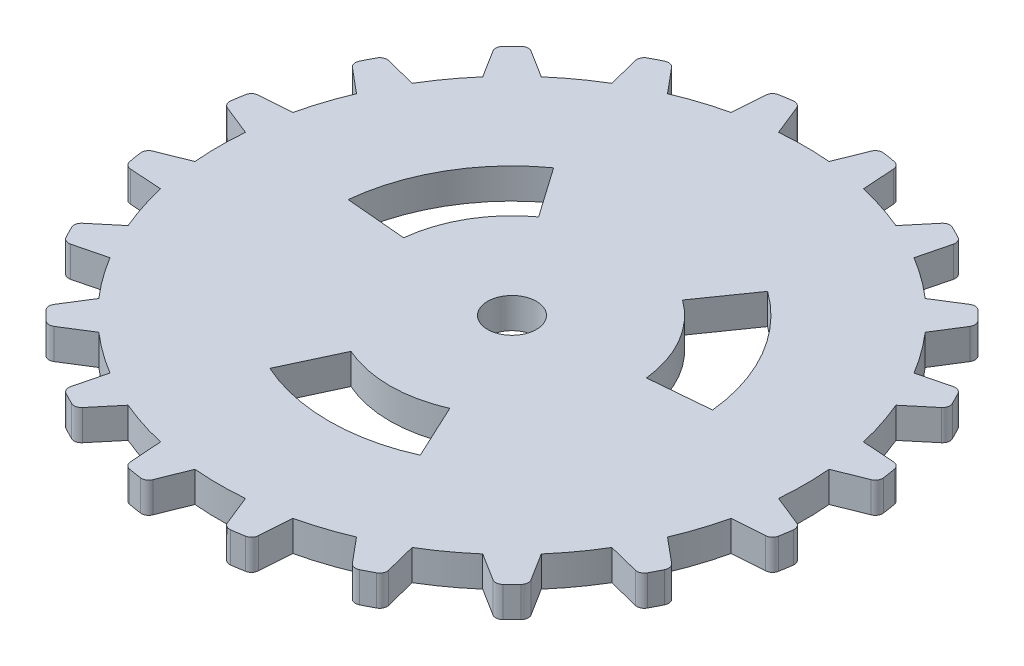
SolidWorks part; units mm, degrees
ref_plane "Front Plane" through (0, 0, 0) normal (0, 0, 1) x (1, 0, 0)
ref_plane "Top Plane" through (0, 0, 0) normal (0, 1, 0) x (1, 0, 0)
ref_plane "Right Plane" through (0, 0, 0) normal (1, 0, 0) x (0, 0, -1)
sketch "Sketch1" plane through (0, 0, 0) normal (0, 1, 0) x (1, 0, 0)
  line L0 (0, 0) -> (0, 28.8903) construction
  line L1 (-3.2322, 26.7985) -> (0, 0)
  line L2 (3.2322, 26.7985) -> (0, 0)
  line L3 (-3.2322, 26.7985) -> (-2.0697, 23.9032)
  line L4 (3.2322, 26.7985) -> (2.0697, 23.9032)
  line L5 (5.2071, 26.4857) -> (5.4181, 23.3729)
  line L6 (11.3552, 24.488) -> (9.3549, 22.0938)
  line L7 (13.1368, 23.5803) -> (12.3756, 20.5547)
  line L8 (18.3667, 19.7806) -> (15.7244, 18.1216)
  line L9 (19.7806, 18.3667) -> (18.1216, 15.7244)
  line L10 (23.5803, 13.1368) -> (20.5547, 12.3756)
  line L11 (24.488, 11.3552) -> (22.0938, 9.3549)
  line L12 (26.4857, 5.2072) -> (23.3729, 5.4181)
  line L13 (26.7985, 3.2322) -> (23.9032, 2.0697)
  line L14 (26.7985, -3.2322) -> (23.9032, -2.0697)
  line L15 (26.4857, -5.2071) -> (23.3729, -5.4181)
  line L16 (24.488, -11.3552) -> (22.0938, -9.3549)
  line L17 (23.5803, -13.1368) -> (20.5547, -12.3756)
  line L18 (19.7806, -18.3667) -> (18.1216, -15.7244)
  line L19 (18.3667, -19.7806) -> (15.7244, -18.1216)
  line L20 (13.1368, -23.5803) -> (12.3756, -20.5547)
  line L21 (11.3552, -24.488) -> (9.3549, -22.0938)
  line L22 (5.2072, -26.4857) -> (5.4181, -23.3729)
  line L23 (3.2322, -26.7985) -> (2.0697, -23.9032)
  line L24 (-3.2322, -26.7985) -> (-2.0697, -23.9032)
  line L25 (-5.2071, -26.4857) -> (-5.4181, -23.3729)
  line L26 (-11.3552, -24.488) -> (-9.3549, -22.0938)
  line L27 (-13.1368, -23.5803) -> (-12.3756, -20.5547)
  line L28 (-18.3667, -19.7806) -> (-15.7244, -18.1216)
  line L29 (-19.7806, -18.3667) -> (-18.1216, -15.7244)
  line L30 (-23.5803, -13.1368) -> (-20.5547, -12.3756)
  line L31 (-24.488, -11.3552) -> (-22.0938, -9.3549)
  line L32 (-26.4857, -5.2072) -> (-23.3729, -5.4181)
  line L33 (-26.7985, -3.2322) -> (-23.9032, -2.0697)
  line L34 (-26.7985, 3.2322) -> (-23.9032, 2.0697)
  line L35 (-26.4857, 5.2071) -> (-23.3729, 5.4181)
  line L36 (-24.488, 11.3552) -> (-22.0938, 9.3549)
  line L37 (-23.5803, 13.1368) -> (-20.5547, 12.3756)
  line L38 (-19.7806, 18.3667) -> (-18.1216, 15.7244)
  line L39 (-18.3667, 19.7806) -> (-15.7244, 18.1216)
  line L40 (-13.1368, 23.5803) -> (-12.3756, 20.5547)
  line L41 (-11.3552, 24.488) -> (-9.3549, 22.0938)
  line L42 (-5.2072, 26.4857) -> (-5.4181, 23.3729)
  line L43 (4.7898, 14.7414) -> (2.7812, 8.5595)
  line L44 (-4.7898, 14.7414) -> (-2.7812, 8.5595)
  line L45 (14.7414, -4.7898) -> (8.5595, -2.7812)
  line L46 (14.7414, 4.7898) -> (8.5595, 2.7812)
  line L47 (-4.7898, -14.7414) -> (-2.7812, -8.5595)
  line L48 (4.7898, -14.7414) -> (2.7812, -8.5595)
  line L49 (-14.7414, 4.7898) -> (-8.5595, 2.7812)
  line L50 (-14.7414, -4.7898) -> (-8.5595, -2.7812)
  circle A0 centre (0, 0) radius 26.9927
  circle A1 centre (0, 0) radius 23.9927
  circle A2 centre (0, 0) radius 9
  circle A3 centre (0, 0) radius 15.5
  point P4 (-3.2322, 26.7985)
  point P7 (3.2322, 26.7985)
  point P9 (-2.0697, 23.9032)
  point P13 (0, 23.9927)
  point P92 (0, 0)
  point P111 (0, 0)
  dimension "D1" = 53.9854
  dimension "D2" = 47.9854
  dimension "D8" = 18
  dimension "D9" = 31
  dimension "D3" = 13.755
  dimension "D4" = 6.877
  dimension "D5" = 15
  dimension "D6" = 15
  dimension "D10" = 18
  dimension "D11" = 18
  dimension "D7" = 20
  dimension "D12" = 4
extrude "Boss-Extrude1" add sketch "Sketch1" against normal blind 2.5 contours A1 L2 L1 | A1 L41 A0 L40 | A1 L1 A0 L42 | A1 L3 L1 | A1 L2 L4 | A1 L5 A0 L2 | A1 L7 A0 L6 | A1 L9 A0 L8 | A1 L11 A0 L10 | A1 L13 A0 L12 | L0 L2 A1 | L1 L0 A1 | A1 L15 A0 L14 | A1 L17 A0 L16 | A1 L19 A0 L18 | A1 L21 A0 L20 | A1 L23 A0 L22 | A1 L25 A0 L24 | A1 L27 A0 L26 | A1 L29 A0 L28 | A1 L31 A0 L30 | A1 L33 A0 L32 | A1 L39 A0 L38 | A1 L37 A0 L36 | A1 L35 A0 L34 | A3
fillet "Fillet1" radius 0.6 40 edges at (-11.3552, -1.25, -24.488) (-18.3667, -1.25, -19.7806) (-26.7985, -1.25, -3.2322) (-13.1368, -1.25, -23.5803) (-19.7806, -1.25, -18.3667) (-23.5803, -1.25, -13.1368) (-24.488, -1.25, -11.3552) (-26.4857, -1.25, -5.2071) (-26.7985, -1.25, 3.2322) (-24.488, -1.25, 11.3552) (-19.7806, -1.25, 18.3667) (-26.4857, -1.25, 5.2072) (-23.5803, -1.25, 13.1368) (-18.3667, -1.25, 19.7806) (-13.1368, -1.25, 23.5803) (-11.3552, -1.25, 24.488) (-5.2071, -1.25, 26.4857) (-3.2322, -1.25, 26.7985) (3.2322, -1.25, 26.7985) (5.2072, -1.25, 26.4857) (11.3552, -1.25, 24.488) (13.1368, -1.25, 23.5803) (18.3667, -1.25, 19.7806) (19.7806, -1.25, 18.3667) (23.5803, -1.25, 13.1368) (24.488, -1.25, 11.3552) (26.4857, -1.25, 5.2071) (26.7985, -1.25, 3.2322) (26.7985, -1.25, -3.2322) (26.4857, -1.25, -5.2072) (24.488, -1.25, -11.3552) (23.5803, -1.25, -13.1368) (19.7806, -1.25, -18.3667) (18.3667, -1.25, -19.7806) (13.1368, -1.25, -23.5803) (11.3552, -1.25, -24.488) (5.2071, -1.25, -26.4857) (3.2322, -1.25, -26.7985) (-5.2072, -1.25, -26.4857) (-3.2322, -1.25, -26.7985)
sketch "Sketch2" plane through (0, -2.5, 0) normal (0, -1, 0) x (1, 0, 0)
  line L0 (14.7414, -4.7898) -> (8.5595, -2.7812) construction
  line L1 (14.7414, 4.7898) -> (8.5595, 2.7812) construction
  line L2 (4.7898, 14.7414) -> (2.7812, 8.5595) construction
  line L3 (-4.7898, 14.7414) -> (-2.7812, 8.5595) construction
  line L4 (-14.7414, 4.7898) -> (-8.5595, 2.7812) construction
  line L5 (-14.7414, -4.7898) -> (-8.5595, -2.7812) construction
  line L6 (-4.7898, -14.7414) -> (-2.7812, -8.5595) construction
  line L7 (4.7898, -14.7414) -> (2.7812, -8.5595) construction
  line L8 (14.7414, -4.7898) -> (8.5595, -2.7812)
  line L9 (14.7414, 4.7898) -> (8.5595, 2.7812)
  line L10 (4.7898, 14.7414) -> (2.7812, 8.5595)
  line L11 (-4.7898, 14.7414) -> (-2.7812, 8.5595)
  line L12 (-14.7414, 4.7898) -> (-8.5595, 2.7812)
  line L13 (-14.7414, -4.7898) -> (-8.5595, -2.7812)
  line L14 (-4.7898, -14.7414) -> (-2.7812, -8.5595)
  line L15 (4.7898, -14.7414) -> (2.7812, -8.5595)
  circle A0 centre (0, 0) radius 9 construction
  circle A1 centre (0, 0) radius 15.5 construction
  circle A2 centre (0, 0) radius 9
  circle A3 centre (0, 0) radius 15.5
extrude "Cut-Extrude1" [suppressed] cut sketch "Sketch2" against normal through all contours L14 A3 L15 A2 | L8 A3 L9 A2 | L10 A3 L11 A2 | L12 A3 L13 A2
sketch "Sketch3" plane through (0, -2.5, 0) normal (0, -1, 0) x (1, 0, 0)
  circle A0 centre (0, 0) radius 2
  dimension "D1" = 4
extrude "Cut-Extrude2" cut sketch "Sketch3" against normal through all
sketch "Sketch4" plane through (0, 0, 0) normal (0, 1, 0) x (1, 0, 0)
  line L0 (0, 0) -> (50.7534, 29.3025) construction
  line L1 (0, 0) -> (0, 45.599) construction
  line L8 (5.8954, 8.0774) -> (8.7636, 12.1737)
  line L9 (9.9429, 1.0668) -> (14.9245, 1.5027)
  line L10 (4.0476, -9.1442) -> (6.1609, -13.6764)
  line L11 (-4.0476, -9.1442) -> (-6.1609, -13.6764)
  line L12 (-9.9429, 1.0668) -> (-14.9245, 1.5027)
  line L13 (-5.8954, 8.0774) -> (-8.7636, 12.1737)
  arc A6 (14.9245, 1.5027) -> (8.7636, 12.1737) centre (0, 0) ccw
  arc A7 (9.9429, 1.0668) -> (5.8954, 8.0774) centre (0, 0) ccw
  arc A8 (-6.1609, -13.6764) -> (6.1609, -13.6764) centre (0, 0) ccw
  arc A9 (-4.0476, -9.1442) -> (4.0476, -9.1442) centre (0, 0) ccw
  arc A10 (-8.7636, 12.1737) -> (-14.9245, 1.5027) centre (0, 0) ccw
  arc A11 (-5.8954, 8.0774) -> (-9.9429, 1.0668) centre (0, 0) ccw
  point P18 (0, 0)
  dimension "D1" = 20
  dimension "D2" = 30
  dimension "D3" = 60
  dimension "D4" = 25
extrude "Cut-Extrude3" cut sketch "Sketch4" against normal blind 10
